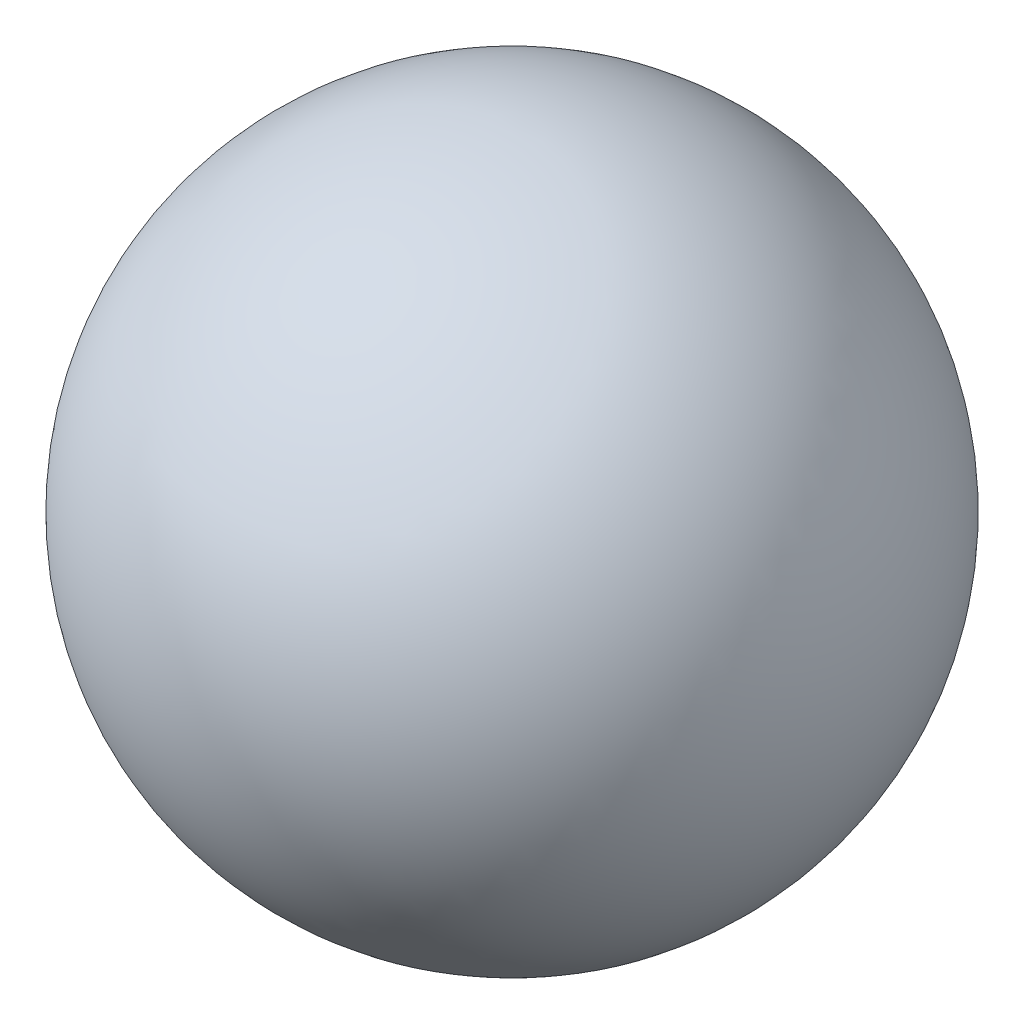
SolidWorks part; units mm, degrees
ref_plane "Front Plane" through (0, 0, 0) normal (0, 0, 1) x (1, 0, 0)
ref_plane "Top Plane" through (0, 0, 0) normal (0, 1, 0) x (1, 0, 0)
ref_plane "Right Plane" through (0, 0, 0) normal (1, 0, 0) x (0, 0, -1)
sketch "Sketch1" plane through (0, 0, 0) normal (0, 0, 1) x (1, 0, 0)
  line L0 (0, 10.8303) -> (0, -12.0981) construction
  line L1 (0, 7.5) -> (0, -7.5)
  arc A0 (0, -7.5) -> (0, 7.5) centre (0, 0) ccw
  dimension "D1" = 15
revolve "Revolve1" add sketch "Sketch1" angle 360 about L0
